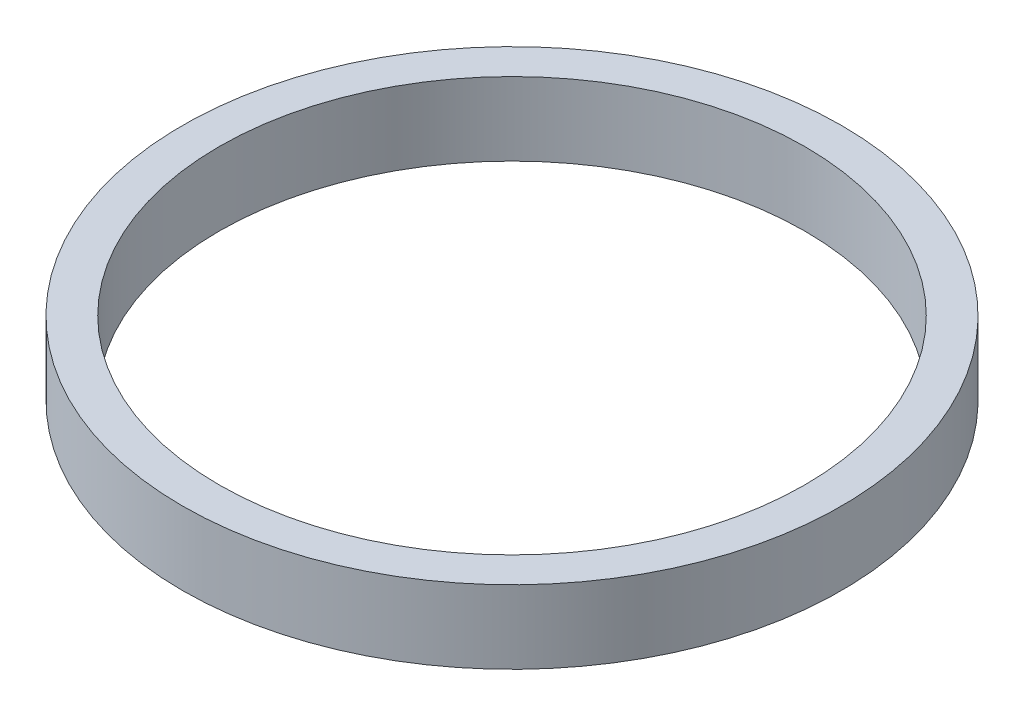
SolidWorks part; units mm, degrees
ref_plane "Front Plane" through (0, 0, 0) normal (0, 0, 1) x (1, 0, 0)
ref_plane "Top Plane" through (0, 0, 0) normal (0, 1, 0) x (1, 0, 0)
ref_plane "Right Plane" through (0, 0, 0) normal (1, 0, 0) x (0, 0, -1)
sketch "Sketch1" plane through (0, 0, 0) normal (0, 1, 0) x (1, 0, 0)
  circle A0 centre (0, 0) radius 45
extrude "Boss-Extrude1" add sketch "Sketch1" along normal blind 10
sketch "Sketch2" plane through (0, 10, 0) normal (0, 1, 0) x (1, 0, 0)
  circle A0 centre (0, 0) radius 40
extrude "Cut-Extrude1" cut sketch "Sketch2" against normal blind 10
